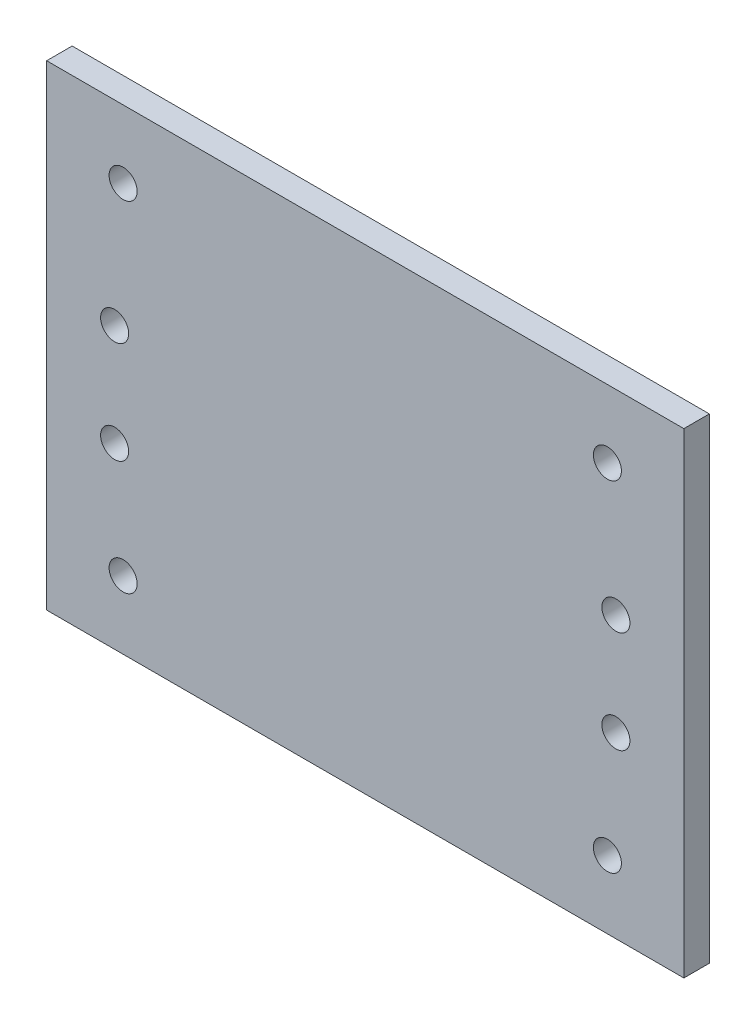
SolidWorks part; units mm, degrees
ref_plane "前视基准面" through (0, 0, 0) normal (0, 0, 1) x (1, 0, 0)
ref_plane "上视基准面" through (0, 0, 0) normal (0, 1, 0) x (1, 0, 0)
ref_plane "右视基准面" through (0, 0, 0) normal (1, 0, 0) x (0, 0, -1)
sketch "草图1" plane through (0, 0, 0) normal (0, 0, 1) x (1, 0, 0)
  line L1 (-37.5, 28) -> (37.5, 28)
  line L2 (-37.5, 28) -> (-37.5, -28)
  line L3 (-37.5, -28) -> (37.5, -28)
  line L4 (37.5, 28) -> (37.5, -28)
  line L5 (-37.5, 28) -> (37.5, -28) construction
  line L6 (-37.5, -28) -> (37.5, 28) construction
  point P0 (0, 0)
  dimension "D1" = 75
  dimension "D2" = 56
extrude "凸台-拉伸1" add sketch "草图1" along normal blind 3
sketch "草图2" plane through (0, 0, 0) normal (0, 0, -1) x (-1, 0, 0)
  line L1 (-28.5, 20) -> (28.5, 20) construction
  line L2 (-28.5, 20) -> (-28.5, -20) construction
  line L3 (-28.5, -20) -> (28.5, -20) construction
  line L4 (28.5, 20) -> (28.5, -20) construction
  line L5 (-28.5, 20) -> (28.5, -20) construction
  line L6 (-28.5, -20) -> (28.5, 20) construction
  circle A0 centre (-28.5, 20) radius 1.65
  circle A1 centre (28.5, 20) radius 1.65
  circle A2 centre (-28.5, -20) radius 1.65
  circle A3 centre (28.5, -20) radius 1.65
  point P0 (0, 0)
  dimension "D3" = 3.3
  dimension "D1" = 57
  dimension "D2" = 40
extrude "切除-拉伸1" cut sketch "草图2" against normal blind 3
sketch "草图4" plane through (0, 0, 0) normal (0, 0, -1) x (-1, 0, 0)
  line L0 (37.5, -28) -> (-37.5, -28) construction
  line L1 (-29.5, 5) -> (29.5, 5) construction
  line L2 (-29.5, 5) -> (-29.5, -7) construction
  line L3 (-29.5, -7) -> (29.5, -7) construction
  line L4 (29.5, 5) -> (29.5, -7) construction
  line L5 (-29.5, 5) -> (29.5, -7) construction
  line L6 (-29.5, -7) -> (29.5, 5) construction
  circle A0 centre (-29.5, 5) radius 1.65
  circle A1 centre (29.5, 5) radius 1.65
  circle A2 centre (-29.5, -7) radius 1.65
  circle A3 centre (29.5, -7) radius 1.65
  point P0 (0, -1)
  dimension "D4" = 3.3
  dimension "D1" = 27
  dimension "D2" = 59
  dimension "D3" = 12
extrude "切除-拉伸3" cut sketch "草图4" against normal blind 8
